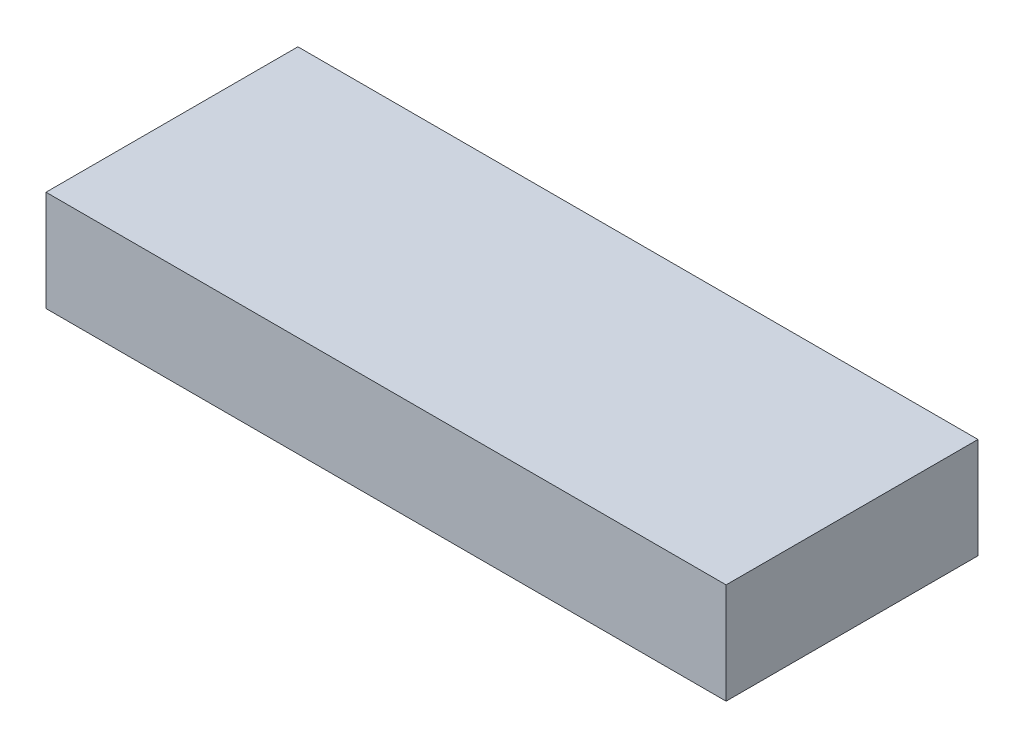
SolidWorks part; units mm, degrees
ref_plane "Front Plane" through (0, 0, 0) normal (0, 0, 1) x (1, 0, 0)
ref_plane "Top Plane" through (0, 0, 0) normal (0, 1, 0) x (1, 0, 0)
ref_plane "Right Plane" through (0, 0, 0) normal (1, 0, 0) x (0, 0, -1)
sketch "Sketch1" plane through (0, 0, 0) normal (0, 1, 0) x (1, 0, 0)
  line L1 (0, 0) -> (68.58, 0)
  line L2 (0, 0) -> (0, 25.4)
  line L3 (0, 25.4) -> (68.58, 25.4)
  line L4 (68.58, 0) -> (68.58, 25.4)
  dimension "D1" = 25.4
  dimension "D2" = 68.58
extrude "Boss-Extrude1" add sketch "Sketch1" along normal blind 10.16
sketch "Sketch2" plane through (0, 0, 0) normal (-1, 0, 0) x (0, 0, 1)
  circle A0 centre (-12.8025, 2.0164) radius 1.1263
extrude "Cut-Extrude1" cut sketch "Sketch2" against normal blind 5.08
